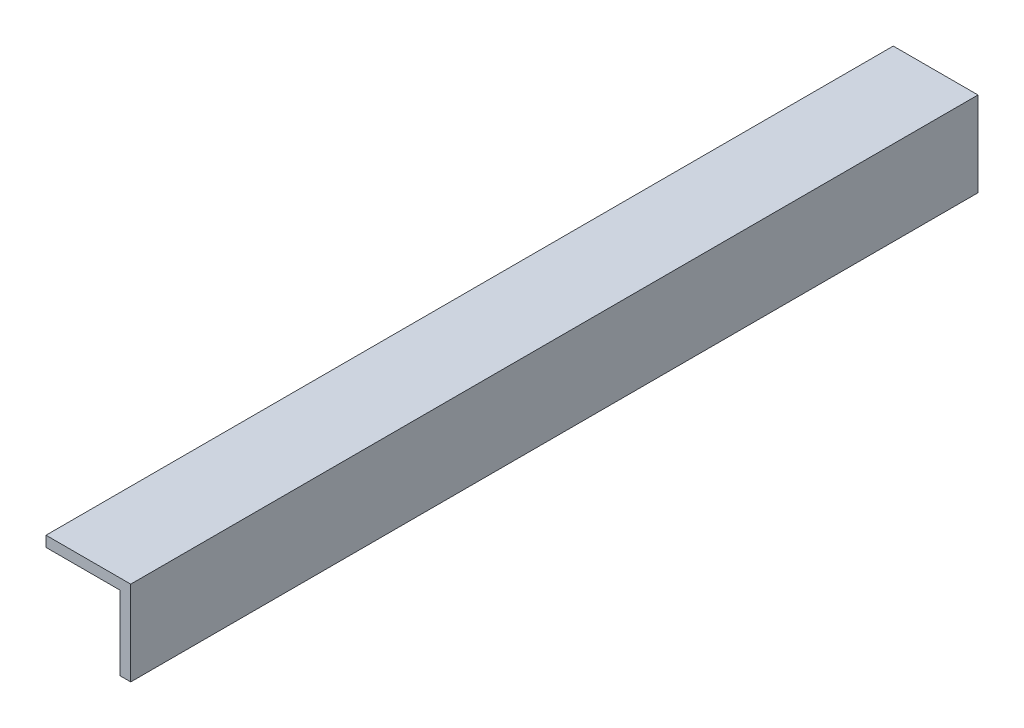
SolidWorks part; units mm, degrees
ref_plane "Front Plane" through (0, 0, 0) normal (0, 0, 1) x (1, 0, 0)
ref_plane "Top Plane" through (0, 0, 0) normal (0, 1, 0) x (1, 0, 0)
ref_plane "Right Plane" through (0, 0, 0) normal (1, 0, 0) x (0, 0, -1)
sketch "Sketch1" plane through (0, 0, 0) normal (0, 0, 1) x (1, 0, 0)
  line L3 (1.9141, 12.7) -> (1.9141, -12.7)
  line L4 (1.9141, -12.7) -> (-1.2609, -12.7)
  line L5 (-1.2609, -12.7) -> (-1.2609, 9.525)
  line L6 (-1.2609, 9.525) -> (-23.4859, 9.525)
  line L7 (-23.4859, 9.525) -> (-23.4859, 12.7)
  line L8 (-23.4859, 12.7) -> (1.9141, 12.7)
  point P1 (1.9141, 0)
  dimension "D1" = 25.4
  dimension "D3" = 3.175
extrude "Boss-Extrude1" add sketch "Sketch1" along normal blind 254
